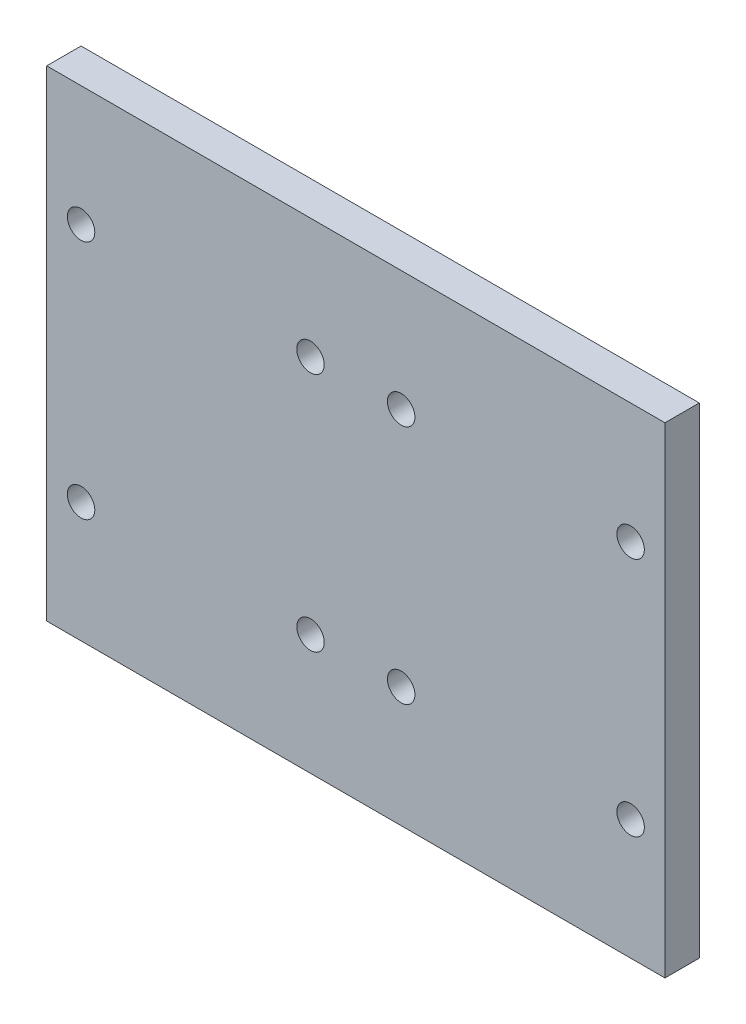
SolidWorks part; units mm, degrees
ref_plane "Front Plane" through (0, 0, 0) normal (0, 0, 1) x (1, 0, 0)
ref_plane "Top Plane" through (0, 0, 0) normal (0, 1, 0) x (1, 0, 0)
ref_plane "Right Plane" through (0, 0, 0) normal (1, 0, 0) x (0, 0, -1)
sketch "Sketch1" plane through (0, 0, 0) normal (0, 0, 1) x (1, 0, 0)
  line L4 (-67.538, 0) -> (61.6563, 0) construction
  line L5 (0, 31.0047) -> (0, -34.6671) construction
  line L6 (-45, 35) -> (-45, -35)
  line L7 (-45, -35) -> (45, -35)
  line L8 (45, -35) -> (45, 35)
  line L9 (45, 35) -> (-45, 35)
  circle A0 centre (-6.6, 17.5) radius 2
  circle A2 centre (6.6, 17.5) radius 2
  circle A3 centre (-6.6, -17.5) radius 2
  circle A4 centre (-40, 17.5) radius 2
  circle A5 centre (-40, -17.5) radius 2
  circle A6 centre (40, 17.5) radius 2
  circle A8 centre (6.6, -17.5) radius 2
  circle A9 centre (40, -17.5) radius 2
  dimension "D1" = 4
  dimension "D2" = 4
  dimension "D3" = 4
  dimension "D4" = 4
  dimension "D5" = 4
  dimension "D6" = 4
  dimension "D7" = 4
  dimension "D10" = 4
  dimension "D8" = 17.5
  dimension "D9" = 33.4
  dimension "D11" = 17.5
  dimension "D12" = 33.4
  dimension "D13" = 33.4
  dimension "D14" = 6.6
  dimension "D15" = 6.6
  dimension "D16" = 33.4
  dimension "D17" = 35
  dimension "D18" = 70
  dimension "D19" = 90
  dimension "D20" = 45
  dimension "D21" = 35
extrude "Boss-Extrude1" add sketch "Sketch1" along normal blind 5
